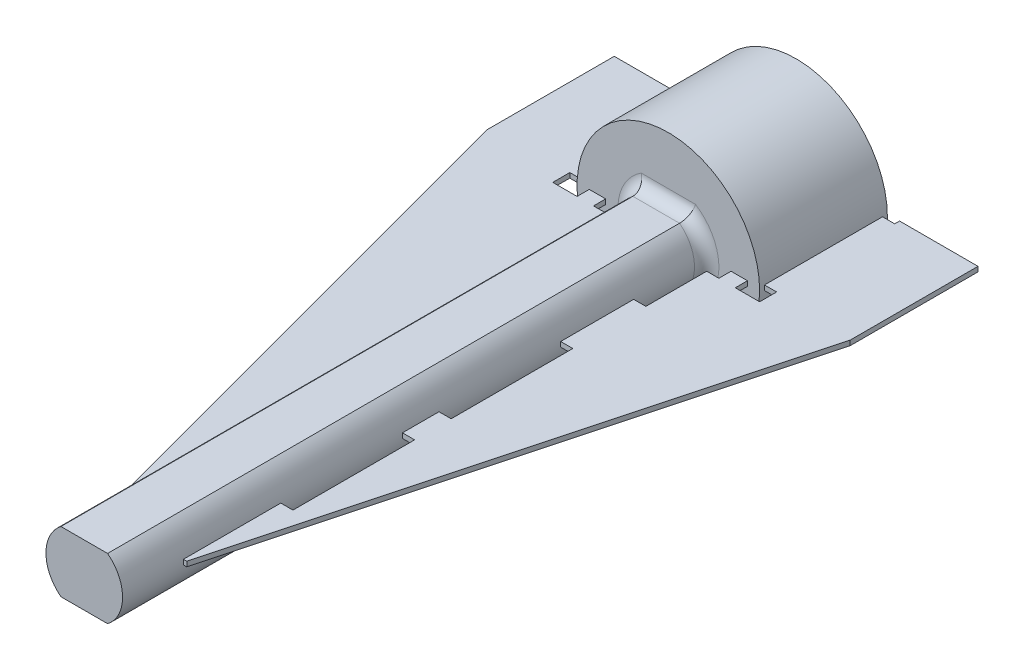
SolidWorks part; units mm, degrees
material "Polylactic Acid (PLA)"
ref_plane "Front Plane" through (0, 0, 0) normal (0, 0, 1) x (1, 0, 0)
ref_plane "Top Plane" through (0, 0, 0) normal (0, 1, 0) x (1, 0, 0)
ref_plane "Right Plane" through (0, 0, 0) normal (1, 0, 0) x (0, 0, -1)
sketch "Sketch2" plane through (0, 0, 0) normal (0, 0, 1) x (1, 0, 0)
  arc A0 (-180.9646, 16.9181) -> (-181.2813, 16.5945) centre (-180.7258, 16.3677) ccw
  arc A1 (-181.2813, 16.5945) -> (-181.4587, 15.6283) centre (-179.0594, 15.6871) ccw
  arc A2 (-181.4587, 15.6283) -> (-180.9368, 15.2683) centre (-178.5779, 19.2465) ccw
  arc A3 (-180.9368, 15.2683) -> (-180.0966, 15.7774) centre (-181.7341, 17.532) ccw
  arc A4 (-180.0966, 15.7774) -> (-179.9066, 16.1884) centre (-180.506, 16.216) ccw
  arc A5 (-179.7695, 16.2766) -> (-179.9066, 16.1884) centre (-179.8067, 16.1838) ccw
  arc A6 (-179.7695, 16.2766) -> (-179.5312, 16.1918) centre (-178.5779, 19.2465) ccw
  arc A7 (-179.4806, 16.0368) -> (-179.5312, 16.1918) centre (-179.561, 16.0963) ccw
  arc A8 (-179.4806, 16.0368) -> (-179.5931, 15.5981) centre (-178.9987, 15.6794) ccw
  arc A9 (-179.5931, 15.5981) -> (-179.2637, 14.6726) centre (-177.2152, 15.9232) ccw
  arc A10 (-179.2637, 14.6726) -> (-178.6317, 14.6218) centre (-178.5779, 19.2465) ccw
  arc A11 (-178.6317, 14.6218) -> (-178.1586, 15.4828) centre (-180.454, 16.1836) ccw
  arc A12 (-178.1586, 15.4828) -> (-178.1996, 15.9338) centre (-178.7324, 15.658) ccw
  arc A13 (-178.1249, 16.0787) -> (-178.1996, 15.9338) centre (-178.1108, 15.9797) ccw
  arc A14 (-178.1249, 16.0787) -> (-177.8761, 16.1244) centre (-178.5779, 19.2465) ccw
  arc A15 (-177.7548, 16.0154) -> (-177.8761, 16.1244) centre (-177.8542, 16.0268) ccw
  arc A16 (-177.7548, 16.0154) -> (-177.6329, 15.5793) centre (-177.1587, 15.9469) ccw
  arc A17 (-177.6329, 15.5793) -> (-176.8848, 14.9425) centre (-175.7362, 17.0498) ccw
  arc A18 (-176.8848, 14.9425) -> (-176.3121, 15.2145) centre (-178.5779, 19.2465) ccw
  arc A19 (-176.3121, 15.2145) -> (-176.3329, 16.1967) centre (-178.6712, 15.6559) ccw
  arc A20 (-176.3329, 16.1967) -> (-176.5939, 16.5668) centre (-176.9175, 16.0615) ccw
  arc A21 (-176.6017, 16.7296) -> (-176.5939, 16.5668) centre (-176.54, 16.651) ccw
  arc A22 (-176.6017, 16.7296) -> (-176.4091, 16.8936) centre (-178.5779, 19.2465) ccw
  arc A23 (-176.2496, 16.8599) -> (-176.4091, 16.8936) centre (-176.3413, 16.8201) ccw
  arc A24 (-176.2496, 16.8599) -> (-175.926, 16.5431) centre (-175.6991, 17.0986) ccw
  arc A25 (-175.926, 16.5431) -> (-174.9597, 16.3657) centre (-175.0185, 18.765) ccw
  arc A26 (-174.9597, 16.3657) -> (-174.5997, 16.8876) centre (-178.5779, 19.2465) ccw
  arc A27 (-174.5997, 16.8876) -> (-175.1088, 17.7278) centre (-176.8634, 16.0903) ccw
  arc A28 (-175.1088, 17.7278) -> (-175.5198, 17.9178) centre (-175.5475, 17.3184) ccw
  arc A29 (-175.608, 18.0549) -> (-175.5198, 17.9178) centre (-175.5152, 18.0177) ccw
  arc A30 (-175.608, 18.0549) -> (-175.5232, 18.2932) centre (-178.5779, 19.2465) ccw
  arc A31 (-175.3682, 18.3438) -> (-175.5232, 18.2932) centre (-175.4277, 18.2635) ccw
  arc A32 (-175.3682, 18.3438) -> (-174.9296, 18.2313) centre (-175.0108, 18.8258) ccw
  arc A33 (-174.9296, 18.2313) -> (-174.004, 18.5608) centre (-175.2546, 20.6092) ccw
  arc A34 (-174.004, 18.5608) -> (-173.9532, 19.1927) centre (-178.5779, 19.2465) ccw
  arc A35 (-173.9532, 19.1927) -> (-174.8142, 19.6658) centre (-175.515, 17.3704) ccw
  arc A36 (-174.8142, 19.6658) -> (-175.2652, 19.6248) centre (-174.9894, 19.092) ccw
  arc A37 (-175.4102, 19.6995) -> (-175.2652, 19.6248) centre (-175.3112, 19.7137) ccw
  arc A38 (-175.4102, 19.6995) -> (-175.4558, 19.9483) centre (-178.5779, 19.2465) ccw
  arc A39 (-175.3469, 20.0696) -> (-175.4558, 19.9483) centre (-175.3583, 19.9702) ccw
  arc A40 (-175.3469, 20.0696) -> (-174.9108, 20.1915) centre (-175.2784, 20.6657) ccw
  arc A41 (-174.9108, 20.1915) -> (-174.274, 20.9396) centre (-176.3812, 22.0882) ccw
  arc A42 (-174.274, 20.9396) -> (-174.5459, 21.5123) centre (-178.5779, 19.2465) ccw
  arc A43 (-174.5459, 21.5123) -> (-175.5282, 21.4915) centre (-174.9873, 19.1532) ccw
  arc A44 (-175.5282, 21.4915) -> (-175.8982, 21.2305) centre (-175.3929, 20.9069) ccw
  arc A45 (-176.0611, 21.2227) -> (-175.8982, 21.2305) centre (-175.9824, 21.2845) ccw
  arc A46 (-176.0611, 21.2227) -> (-176.225, 21.4153) centre (-178.5779, 19.2465) ccw
  arc A47 (-176.1913, 21.5749) -> (-176.225, 21.4153) centre (-176.1515, 21.4831) ccw
  arc A48 (-176.1913, 21.5749) -> (-175.8746, 21.8985) centre (-176.43, 22.1253) ccw
  arc A49 (-175.8746, 21.8985) -> (-175.6971, 22.8647) centre (-178.0964, 22.8059) ccw
  arc A50 (-175.6971, 22.8647) -> (-176.219, 23.2247) centre (-178.5779, 19.2465) ccw
  arc A51 (-176.219, 23.2247) -> (-177.0592, 22.7156) centre (-175.4217, 20.961) ccw
  arc A52 (-177.0592, 22.7156) -> (-177.2492, 22.3046) centre (-176.6499, 22.277) ccw
  arc A53 (-177.3864, 22.2164) -> (-177.2492, 22.3046) centre (-177.3491, 22.3092) ccw
  arc A54 (-177.3864, 22.2164) -> (-177.6247, 22.3012) centre (-178.5779, 19.2465) ccw
  arc A55 (-177.6752, 22.4562) -> (-177.6247, 22.3012) centre (-177.5949, 22.3967) ccw
  arc A56 (-177.6752, 22.4562) -> (-177.5627, 22.8948) centre (-178.1572, 22.8136) ccw
  arc A57 (-177.5627, 22.8948) -> (-177.8922, 23.8204) centre (-179.9406, 22.5698) ccw
  arc A58 (-177.8922, 23.8204) -> (-178.5242, 23.8712) centre (-178.5779, 19.2465) ccw
  arc A59 (-178.5242, 23.8712) -> (-178.9973, 23.0102) centre (-176.7018, 22.3094) ccw
  arc A60 (-178.9973, 23.0102) -> (-178.9563, 22.5592) centre (-178.4234, 22.835) ccw
  arc A61 (-179.0309, 22.4143) -> (-178.9563, 22.5592) centre (-179.0451, 22.5133) ccw
  arc A62 (-179.0309, 22.4143) -> (-179.2797, 22.3686) centre (-178.5779, 19.2465) ccw
  arc A63 (-179.401, 22.4776) -> (-179.2797, 22.3686) centre (-179.3017, 22.4661) ccw
  arc A64 (-179.401, 22.4776) -> (-179.5229, 22.9137) centre (-179.9971, 22.546) ccw
  arc A65 (-179.5229, 22.9137) -> (-180.271, 23.5505) centre (-181.4197, 21.4432) ccw
  arc A66 (-180.271, 23.5505) -> (-180.8437, 23.2785) centre (-178.5779, 19.2465) ccw
  arc A67 (-180.8437, 23.2785) -> (-180.8229, 22.2963) centre (-178.4846, 22.8371) ccw
  arc A68 (-180.8229, 22.2963) -> (-180.562, 21.9262) centre (-180.2383, 22.4315) ccw
  arc A69 (-180.5541, 21.7634) -> (-180.562, 21.9262) centre (-180.6159, 21.842) ccw
  arc A70 (-180.5541, 21.7634) -> (-180.7468, 21.5994) centre (-178.5779, 19.2465) ccw
  arc A71 (-180.9063, 21.6331) -> (-180.7468, 21.5994) centre (-180.8145, 21.6729) ccw
  arc A72 (-180.9063, 21.6331) -> (-181.2299, 21.9499) centre (-181.4567, 21.3944) ccw
  arc A73 (-181.2299, 21.9499) -> (-182.1962, 22.1273) centre (-182.1373, 19.728) ccw
  arc A74 (-182.1962, 22.1273) -> (-182.5561, 21.6054) centre (-178.5779, 19.2465) ccw
  arc A75 (-182.5561, 21.6054) -> (-182.047, 20.7652) centre (-180.2924, 22.4027) ccw
  arc A76 (-182.047, 20.7652) -> (-181.636, 20.5752) centre (-181.6084, 21.1746) ccw
  arc A77 (-181.5478, 20.4381) -> (-181.636, 20.5752) centre (-181.6406, 20.4753) ccw
  arc A78 (-181.5478, 20.4381) -> (-181.6326, 20.1997) centre (-178.5779, 19.2465) ccw
  arc A79 (-181.7877, 20.1492) -> (-181.6326, 20.1997) centre (-181.7281, 20.2295) ccw
  arc A80 (-181.7877, 20.1492) -> (-182.2263, 20.2617) centre (-182.145, 19.6672) ccw
  arc A81 (-182.2263, 20.2617) -> (-183.1518, 19.9322) centre (-181.9012, 17.8838) ccw
  arc A82 (-183.1518, 19.9322) -> (-183.2026, 19.3002) centre (-178.5779, 19.2465) ccw
  arc A83 (-183.2026, 19.3002) -> (-182.3416, 18.8272) centre (-181.6408, 21.1226) ccw
  arc A84 (-182.3416, 18.8272) -> (-181.8906, 18.8681) centre (-182.1664, 19.401) ccw
  arc A85 (-181.7457, 18.7935) -> (-181.8906, 18.8681) centre (-181.8447, 18.7793) ccw
  arc A86 (-181.7457, 18.7935) -> (-181.7, 18.5447) centre (-178.5779, 19.2465) ccw
  arc A87 (-181.809, 18.4234) -> (-181.7, 18.5447) centre (-181.7976, 18.5227) ccw
  arc A88 (-181.809, 18.4234) -> (-182.2451, 18.3015) centre (-181.8775, 17.8273) ccw
  arc A89 (-182.2451, 18.3015) -> (-182.8819, 17.5534) centre (-180.7746, 16.4047) ccw
  arc A90 (-182.8819, 17.5534) -> (-182.6099, 16.9807) centre (-178.5779, 19.2465) ccw
  arc A91 (-182.6099, 16.9807) -> (-181.6277, 17.0015) centre (-182.1685, 19.3398) ccw
  arc A92 (-181.6277, 17.0015) -> (-181.2576, 17.2625) centre (-181.7629, 17.5861) ccw
  arc A93 (-181.0948, 17.2703) -> (-181.2576, 17.2625) centre (-181.1734, 17.2085) ccw
  arc A94 (-181.0948, 17.2703) -> (-180.9308, 17.0777) centre (-178.5779, 19.2465) ccw
  arc A95 (-180.9646, 16.9181) -> (-180.9308, 17.0777) centre (-181.0043, 17.0099) ccw
  arc A96 (-180.9248, 16.8264) -> (-181.1887, 16.5567) centre (-180.7258, 16.3677) ccw
  arc A97 (-181.1887, 16.5567) -> (-181.3594, 15.6773) centre (-179.0594, 15.6871) ccw
  arc A98 (-181.3594, 15.6773) -> (-180.9262, 15.3785) centre (-178.5779, 19.2465) ccw
  arc A99 (-180.9262, 15.3785) -> (-180.1648, 15.8505) centre (-181.7341, 17.532) ccw
  arc A100 (-180.1648, 15.8505) -> (-180.0065, 16.193) centre (-180.506, 16.216) ccw
  arc A101 (-179.7323, 16.3694) -> (-180.0065, 16.193) centre (-179.8067, 16.1838) ccw
  arc A102 (-179.7323, 16.3694) -> (-179.5014, 16.2872) centre (-178.5779, 19.2465) ccw
  arc A103 (-179.4003, 15.9772) -> (-179.5014, 16.2872) centre (-179.561, 16.0963) ccw
  arc A104 (-179.4003, 15.9772) -> (-179.494, 15.6117) centre (-178.9987, 15.6794) ccw
  arc A105 (-179.494, 15.6117) -> (-179.2022, 14.7648) centre (-177.2152, 15.9232) ccw
  arc A106 (-179.2022, 14.7648) -> (-178.6776, 14.7226) centre (-178.5779, 19.2465) ccw
  arc A107 (-178.6776, 14.7226) -> (-178.2542, 15.512) centre (-180.454, 16.1836) ccw
  arc A108 (-178.2542, 15.512) -> (-178.2884, 15.8878) centre (-178.7324, 15.658) ccw
  arc A109 (-178.1391, 16.1777) -> (-178.2884, 15.8878) centre (-178.1108, 15.9797) ccw
  arc A110 (-178.1391, 16.1777) -> (-177.898, 16.222) centre (-178.5779, 19.2465) ccw
  arc A111 (-177.6555, 16.004) -> (-177.898, 16.222) centre (-177.8542, 16.0268) ccw
  arc A112 (-177.6555, 16.004) -> (-177.5539, 15.6406) centre (-177.1587, 15.9469) ccw
  arc A113 (-177.5539, 15.6406) -> (-176.8777, 15.0531) centre (-175.7362, 17.0498) ccw
  arc A114 (-176.8777, 15.0531) -> (-176.4023, 15.2788) centre (-178.5779, 19.2465) ccw
  arc A115 (-176.4023, 15.2788) -> (-176.4304, 16.1742) centre (-178.6712, 15.6559) ccw
  arc A116 (-176.4304, 16.1742) -> (-176.6478, 16.4826) centre (-176.9175, 16.0615) ccw
  arc A117 (-176.6635, 16.8083) -> (-176.6478, 16.4826) centre (-176.54, 16.651) ccw
  arc A118 (-176.6635, 16.8083) -> (-176.4769, 16.9671) centre (-178.5779, 19.2465) ccw
  arc A119 (-176.1578, 16.8996) -> (-176.4769, 16.9671) centre (-176.3413, 16.8201) ccw
  arc A120 (-176.1578, 16.8996) -> (-175.8881, 16.6357) centre (-175.6991, 17.0986) ccw
  arc A121 (-175.8881, 16.6357) -> (-175.0088, 16.465) centre (-175.0185, 18.765) ccw
  arc A122 (-175.0088, 16.465) -> (-174.71, 16.8982) centre (-178.5779, 19.2465) ccw
  arc A123 (-174.71, 16.8982) -> (-175.1819, 17.6596) centre (-176.8634, 16.0903) ccw
  arc A124 (-175.1819, 17.6596) -> (-175.5244, 17.8179) centre (-175.5475, 17.3184) ccw
  arc A125 (-175.7009, 18.0922) -> (-175.5244, 17.8179) centre (-175.5152, 18.0177) ccw
  arc A126 (-175.7009, 18.0922) -> (-175.6187, 18.323) centre (-178.5779, 19.2465) ccw
  arc A127 (-175.3086, 18.4241) -> (-175.6187, 18.323) centre (-175.4277, 18.2635) ccw
  arc A128 (-175.3086, 18.4241) -> (-174.9431, 18.3304) centre (-175.0108, 18.8258) ccw
  arc A129 (-174.9431, 18.3304) -> (-174.0962, 18.6222) centre (-175.2546, 20.6092) ccw
  arc A130 (-174.0962, 18.6222) -> (-174.054, 19.1468) centre (-178.5779, 19.2465) ccw
  arc A131 (-174.054, 19.1468) -> (-174.8434, 19.5702) centre (-175.515, 17.3704) ccw
  arc A132 (-174.8434, 19.5702) -> (-175.2192, 19.536) centre (-174.9894, 19.092) ccw
  arc A133 (-175.5091, 19.6853) -> (-175.2192, 19.536) centre (-175.3112, 19.7137) ccw
  arc A134 (-175.5091, 19.6853) -> (-175.5534, 19.9264) centre (-178.5779, 19.2465) ccw
  arc A135 (-175.3354, 20.1689) -> (-175.5534, 19.9264) centre (-175.3583, 19.9702) ccw
  arc A136 (-175.3354, 20.1689) -> (-174.972, 20.2705) centre (-175.2784, 20.6657) ccw
  arc A137 (-174.972, 20.2705) -> (-174.3845, 20.9467) centre (-176.3812, 22.0882) ccw
  arc A138 (-174.3845, 20.9467) -> (-174.6103, 21.4221) centre (-178.5779, 19.2465) ccw
  arc A139 (-174.6103, 21.4221) -> (-175.5056, 21.3941) centre (-174.9873, 19.1532) ccw
  arc A140 (-175.5056, 21.3941) -> (-175.814, 21.1766) centre (-175.3929, 20.9069) ccw
  arc A141 (-176.1397, 21.1609) -> (-175.814, 21.1766) centre (-175.9824, 21.2845) ccw
  arc A142 (-176.1397, 21.1609) -> (-176.2986, 21.3476) centre (-178.5779, 19.2465) ccw
  arc A143 (-176.2311, 21.6666) -> (-176.2986, 21.3476) centre (-176.1515, 21.4831) ccw
  arc A144 (-176.2311, 21.6666) -> (-175.9671, 21.9363) centre (-176.43, 22.1253) ccw
  arc A145 (-175.9671, 21.9363) -> (-175.7964, 22.8156) centre (-178.0964, 22.8059) ccw
  arc A146 (-175.7964, 22.8156) -> (-176.2296, 23.1145) centre (-178.5779, 19.2465) ccw
  arc A147 (-176.2296, 23.1145) -> (-176.991, 22.6425) centre (-175.4217, 20.961) ccw
  arc A148 (-176.991, 22.6425) -> (-177.1493, 22.3) centre (-176.6499, 22.277) ccw
  arc A149 (-177.4236, 22.1236) -> (-177.1493, 22.3) centre (-177.3491, 22.3092) ccw
  arc A150 (-177.4236, 22.1236) -> (-177.6545, 22.2058) centre (-178.5779, 19.2465) ccw
  arc A151 (-177.7555, 22.5158) -> (-177.6545, 22.2058) centre (-177.5949, 22.3967) ccw
  arc A152 (-177.7555, 22.5158) -> (-177.6618, 22.8813) centre (-178.1572, 22.8136) ccw
  arc A153 (-177.6618, 22.8813) -> (-177.9536, 23.7282) centre (-179.9406, 22.5698) ccw
  arc A154 (-177.9536, 23.7282) -> (-178.4782, 23.7704) centre (-178.5779, 19.2465) ccw
  arc A155 (-178.4782, 23.7704) -> (-178.9016, 22.981) centre (-176.7018, 22.3094) ccw
  arc A156 (-178.9016, 22.981) -> (-178.8675, 22.6052) centre (-178.4234, 22.835) ccw
  arc A157 (-179.0168, 22.3153) -> (-178.8675, 22.6052) centre (-179.0451, 22.5133) ccw
  arc A158 (-179.0168, 22.3153) -> (-179.2578, 22.271) centre (-178.5779, 19.2465) ccw
  arc A159 (-179.5004, 22.489) -> (-179.2578, 22.271) centre (-179.3017, 22.4661) ccw
  arc A160 (-179.5004, 22.489) -> (-179.6019, 22.8524) centre (-179.9971, 22.546) ccw
  arc A161 (-179.6019, 22.8524) -> (-180.2781, 23.4399) centre (-181.4197, 21.4432) ccw
  arc A162 (-180.2781, 23.4399) -> (-180.7535, 23.2142) centre (-178.5779, 19.2465) ccw
  arc A163 (-180.7535, 23.2142) -> (-180.7255, 22.3188) centre (-178.4846, 22.8371) ccw
  arc A164 (-180.7255, 22.3188) -> (-180.508, 22.0104) centre (-180.2383, 22.4315) ccw
  arc A165 (-180.4924, 21.6847) -> (-180.508, 22.0104) centre (-180.6159, 21.842) ccw
  arc A166 (-180.4924, 21.6847) -> (-180.679, 21.5259) centre (-178.5779, 19.2465) ccw
  arc A167 (-180.998, 21.5933) -> (-180.679, 21.5259) centre (-180.8145, 21.6729) ccw
  arc A168 (-180.998, 21.5933) -> (-181.2677, 21.8573) centre (-181.4567, 21.3944) ccw
  arc A169 (-181.2677, 21.8573) -> (-182.1471, 22.028) centre (-182.1373, 19.728) ccw
  arc A170 (-182.1471, 22.028) -> (-182.4459, 21.5948) centre (-178.5779, 19.2465) ccw
  arc A171 (-182.4459, 21.5948) -> (-181.9739, 20.8334) centre (-180.2924, 22.4027) ccw
  arc A172 (-181.9739, 20.8334) -> (-181.6314, 20.6751) centre (-181.6084, 21.1746) ccw
  arc A173 (-181.455, 20.4008) -> (-181.6314, 20.6751) centre (-181.6406, 20.4753) ccw
  arc A174 (-181.455, 20.4008) -> (-181.5372, 20.17) centre (-178.5779, 19.2465) ccw
  arc A175 (-181.8472, 20.0689) -> (-181.5372, 20.17) centre (-181.7281, 20.2295) ccw
  arc A176 (-181.8472, 20.0689) -> (-182.2127, 20.1626) centre (-182.145, 19.6672) ccw
  arc A177 (-182.2127, 20.1626) -> (-183.0597, 19.8708) centre (-181.9012, 17.8838) ccw
  arc A178 (-183.0597, 19.8708) -> (-183.1018, 19.3462) centre (-178.5779, 19.2465) ccw
  arc A179 (-183.1018, 19.3462) -> (-182.3124, 18.9228) centre (-181.6408, 21.1226) ccw
  arc A180 (-182.3124, 18.9228) -> (-181.9366, 18.9569) centre (-182.1664, 19.401) ccw
  arc A181 (-181.6467, 18.8076) -> (-181.9366, 18.9569) centre (-181.8447, 18.7793) ccw
  arc A182 (-181.6467, 18.8076) -> (-181.6024, 18.5666) centre (-178.5779, 19.2465) ccw
  arc A183 (-181.8204, 18.324) -> (-181.6024, 18.5666) centre (-181.7976, 18.5227) ccw
  arc A184 (-181.8204, 18.324) -> (-182.1838, 18.2225) centre (-181.8775, 17.8273) ccw
  arc A185 (-182.1838, 18.2225) -> (-182.7714, 17.5463) centre (-180.7746, 16.4047) ccw
  arc A186 (-182.7714, 17.5463) -> (-182.5456, 17.0709) centre (-178.5779, 19.2465) ccw
  arc A187 (-182.5456, 17.0709) -> (-181.6502, 17.0989) centre (-182.1685, 19.3398) ccw
  arc A188 (-181.6502, 17.0989) -> (-181.3419, 17.3164) centre (-181.7629, 17.5861) ccw
  arc A189 (-181.0161, 17.332) -> (-181.3419, 17.3164) centre (-181.1734, 17.2085) ccw
  arc A190 (-181.0161, 17.332) -> (-180.8573, 17.1454) centre (-178.5779, 19.2465) ccw
  arc A191 (-180.9248, 16.8264) -> (-180.8573, 17.1454) centre (-181.0043, 17.0099) ccw
  arc A192 (-180.9248, 16.8264) -> (-181.1887, 16.5567) centre (-180.7258, 16.3677) ccw construction
  arc A193 (-181.1887, 16.5567) -> (-181.3594, 15.6773) centre (-179.0594, 15.6871) ccw construction
  arc A194 (-181.3594, 15.6773) -> (-180.9262, 15.3785) centre (-178.5779, 19.2465) ccw construction
  arc A195 (-180.9262, 15.3785) -> (-180.1648, 15.8505) centre (-181.7341, 17.532) ccw construction
  arc A196 (-180.1648, 15.8505) -> (-180.0065, 16.193) centre (-180.506, 16.216) ccw construction
  arc A197 (-179.7323, 16.3694) -> (-180.0065, 16.193) centre (-179.8067, 16.1838) ccw construction
  arc A198 (-179.7323, 16.3694) -> (-179.5014, 16.2872) centre (-178.5779, 19.2465) ccw construction
  arc A199 (-179.4003, 15.9772) -> (-179.5014, 16.2872) centre (-179.561, 16.0963) ccw construction
  arc A200 (-179.4003, 15.9772) -> (-179.494, 15.6117) centre (-178.9987, 15.6794) ccw construction
  arc A201 (-179.494, 15.6117) -> (-179.2022, 14.7648) centre (-177.2152, 15.9232) ccw construction
  arc A202 (-179.2022, 14.7648) -> (-178.6776, 14.7226) centre (-178.5779, 19.2465) ccw construction
  arc A203 (-178.6776, 14.7226) -> (-178.2542, 15.512) centre (-180.454, 16.1836) ccw construction
  arc A204 (-178.2542, 15.512) -> (-178.2884, 15.8878) centre (-178.7324, 15.658) ccw construction
  arc A205 (-178.1391, 16.1777) -> (-178.2884, 15.8878) centre (-178.1108, 15.9797) ccw construction
  arc A206 (-178.1391, 16.1777) -> (-177.898, 16.222) centre (-178.5779, 19.2465) ccw construction
  arc A207 (-177.6555, 16.004) -> (-177.898, 16.222) centre (-177.8542, 16.0268) ccw construction
  arc A208 (-177.6555, 16.004) -> (-177.5539, 15.6406) centre (-177.1587, 15.9469) ccw construction
  arc A209 (-177.5539, 15.6406) -> (-176.8777, 15.0531) centre (-175.7362, 17.0498) ccw construction
  arc A210 (-176.8777, 15.0531) -> (-176.4023, 15.2788) centre (-178.5779, 19.2465) ccw construction
  arc A211 (-176.4023, 15.2788) -> (-176.4304, 16.1742) centre (-178.6712, 15.6559) ccw construction
  arc A212 (-176.4304, 16.1742) -> (-176.6478, 16.4826) centre (-176.9175, 16.0615) ccw construction
  arc A213 (-176.6635, 16.8083) -> (-176.6478, 16.4826) centre (-176.54, 16.651) ccw construction
  arc A214 (-176.6635, 16.8083) -> (-176.4769, 16.9671) centre (-178.5779, 19.2465) ccw construction
  arc A215 (-176.1578, 16.8996) -> (-176.4769, 16.9671) centre (-176.3413, 16.8201) ccw construction
  arc A216 (-176.1578, 16.8996) -> (-175.8881, 16.6357) centre (-175.6991, 17.0986) ccw construction
  arc A217 (-175.8881, 16.6357) -> (-175.0088, 16.465) centre (-175.0185, 18.765) ccw construction
  arc A218 (-175.0088, 16.465) -> (-174.71, 16.8982) centre (-178.5779, 19.2465) ccw construction
  arc A219 (-174.71, 16.8982) -> (-175.1819, 17.6596) centre (-176.8634, 16.0903) ccw construction
  arc A220 (-175.1819, 17.6596) -> (-175.5244, 17.8179) centre (-175.5475, 17.3184) ccw construction
  arc A221 (-175.7009, 18.0922) -> (-175.5244, 17.8179) centre (-175.5152, 18.0177) ccw construction
  arc A222 (-175.7009, 18.0922) -> (-175.6187, 18.323) centre (-178.5779, 19.2465) ccw construction
  arc A223 (-175.3086, 18.4241) -> (-175.6187, 18.323) centre (-175.4277, 18.2635) ccw construction
  arc A224 (-175.3086, 18.4241) -> (-174.9431, 18.3304) centre (-175.0108, 18.8258) ccw construction
  arc A225 (-174.9431, 18.3304) -> (-174.0962, 18.6222) centre (-175.2546, 20.6092) ccw construction
  arc A226 (-174.0962, 18.6222) -> (-174.054, 19.1468) centre (-178.5779, 19.2465) ccw construction
  arc A227 (-174.054, 19.1468) -> (-174.8434, 19.5702) centre (-175.515, 17.3704) ccw construction
  arc A228 (-174.8434, 19.5702) -> (-175.2192, 19.536) centre (-174.9894, 19.092) ccw construction
  arc A229 (-175.5091, 19.6853) -> (-175.2192, 19.536) centre (-175.3112, 19.7137) ccw construction
  arc A230 (-175.5091, 19.6853) -> (-175.5534, 19.9264) centre (-178.5779, 19.2465) ccw construction
  arc A231 (-175.3354, 20.1689) -> (-175.5534, 19.9264) centre (-175.3583, 19.9702) ccw construction
  arc A232 (-175.3354, 20.1689) -> (-174.972, 20.2705) centre (-175.2784, 20.6657) ccw construction
  arc A233 (-174.972, 20.2705) -> (-174.3845, 20.9467) centre (-176.3812, 22.0882) ccw construction
  arc A234 (-174.3845, 20.9467) -> (-174.6103, 21.4221) centre (-178.5779, 19.2465) ccw construction
  arc A235 (-174.6103, 21.4221) -> (-175.5056, 21.3941) centre (-174.9873, 19.1532) ccw construction
  arc A236 (-175.5056, 21.3941) -> (-175.814, 21.1766) centre (-175.3929, 20.9069) ccw construction
  arc A237 (-176.1397, 21.1609) -> (-175.814, 21.1766) centre (-175.9824, 21.2845) ccw construction
  arc A238 (-176.1397, 21.1609) -> (-176.2986, 21.3476) centre (-178.5779, 19.2465) ccw construction
  arc A239 (-176.2311, 21.6666) -> (-176.2986, 21.3476) centre (-176.1515, 21.4831) ccw construction
  arc A240 (-176.2311, 21.6666) -> (-175.9671, 21.9363) centre (-176.43, 22.1253) ccw construction
  arc A241 (-175.9671, 21.9363) -> (-175.7964, 22.8156) centre (-178.0964, 22.8059) ccw construction
  arc A242 (-175.7964, 22.8156) -> (-176.2296, 23.1145) centre (-178.5779, 19.2465) ccw construction
  arc A243 (-176.2296, 23.1145) -> (-176.991, 22.6425) centre (-175.4217, 20.961) ccw construction
  arc A244 (-176.991, 22.6425) -> (-177.1493, 22.3) centre (-176.6499, 22.277) ccw construction
  arc A245 (-177.4236, 22.1236) -> (-177.1493, 22.3) centre (-177.3491, 22.3092) ccw construction
  arc A246 (-177.4236, 22.1236) -> (-177.6545, 22.2058) centre (-178.5779, 19.2465) ccw construction
  arc A247 (-177.7555, 22.5158) -> (-177.6545, 22.2058) centre (-177.5949, 22.3967) ccw construction
  arc A248 (-177.7555, 22.5158) -> (-177.6618, 22.8813) centre (-178.1572, 22.8136) ccw construction
  arc A249 (-177.6618, 22.8813) -> (-177.9536, 23.7282) centre (-179.9406, 22.5698) ccw construction
  arc A250 (-177.9536, 23.7282) -> (-178.4782, 23.7704) centre (-178.5779, 19.2465) ccw construction
  arc A251 (-178.4782, 23.7704) -> (-178.9016, 22.981) centre (-176.7018, 22.3094) ccw construction
  arc A252 (-178.9016, 22.981) -> (-178.8675, 22.6052) centre (-178.4234, 22.835) ccw construction
  arc A253 (-179.0168, 22.3153) -> (-178.8675, 22.6052) centre (-179.0451, 22.5133) ccw construction
  arc A254 (-179.0168, 22.3153) -> (-179.2578, 22.271) centre (-178.5779, 19.2465) ccw construction
  arc A255 (-179.5004, 22.489) -> (-179.2578, 22.271) centre (-179.3017, 22.4661) ccw construction
  arc A256 (-179.5004, 22.489) -> (-179.6019, 22.8524) centre (-179.9971, 22.546) ccw construction
  arc A257 (-179.6019, 22.8524) -> (-180.2781, 23.4399) centre (-181.4197, 21.4432) ccw construction
  arc A258 (-180.2781, 23.4399) -> (-180.7535, 23.2142) centre (-178.5779, 19.2465) ccw construction
  arc A259 (-180.7535, 23.2142) -> (-180.7255, 22.3188) centre (-178.4846, 22.8371) ccw construction
  arc A260 (-180.7255, 22.3188) -> (-180.508, 22.0104) centre (-180.2383, 22.4315) ccw construction
  arc A261 (-180.4924, 21.6847) -> (-180.508, 22.0104) centre (-180.6159, 21.842) ccw construction
  arc A262 (-180.4924, 21.6847) -> (-180.679, 21.5259) centre (-178.5779, 19.2465) ccw construction
  arc A263 (-180.998, 21.5933) -> (-180.679, 21.5259) centre (-180.8145, 21.6729) ccw construction
  arc A264 (-180.998, 21.5933) -> (-181.2677, 21.8573) centre (-181.4567, 21.3944) ccw construction
  arc A265 (-181.2677, 21.8573) -> (-182.1471, 22.028) centre (-182.1373, 19.728) ccw construction
  arc A266 (-182.1471, 22.028) -> (-182.4459, 21.5948) centre (-178.5779, 19.2465) ccw construction
  arc A267 (-182.4459, 21.5948) -> (-181.9739, 20.8334) centre (-180.2924, 22.4027) ccw construction
  arc A268 (-181.9739, 20.8334) -> (-181.6314, 20.6751) centre (-181.6084, 21.1746) ccw construction
  arc A269 (-181.455, 20.4008) -> (-181.6314, 20.6751) centre (-181.6406, 20.4753) ccw construction
  arc A270 (-181.455, 20.4008) -> (-181.5372, 20.17) centre (-178.5779, 19.2465) ccw construction
  arc A271 (-181.8472, 20.0689) -> (-181.5372, 20.17) centre (-181.7281, 20.2295) ccw construction
  arc A272 (-181.8472, 20.0689) -> (-182.2127, 20.1626) centre (-182.145, 19.6672) ccw construction
  arc A273 (-182.2127, 20.1626) -> (-183.0597, 19.8708) centre (-181.9012, 17.8838) ccw construction
  arc A274 (-183.0597, 19.8708) -> (-183.1018, 19.3462) centre (-178.5779, 19.2465) ccw construction
  arc A275 (-183.1018, 19.3462) -> (-182.3124, 18.9228) centre (-181.6408, 21.1226) ccw construction
  arc A276 (-182.3124, 18.9228) -> (-181.9366, 18.9569) centre (-182.1664, 19.401) ccw construction
  arc A277 (-181.6467, 18.8076) -> (-181.9366, 18.9569) centre (-181.8447, 18.7793) ccw construction
  arc A278 (-181.6467, 18.8076) -> (-181.6024, 18.5666) centre (-178.5779, 19.2465) ccw construction
  arc A279 (-181.8204, 18.324) -> (-181.6024, 18.5666) centre (-181.7976, 18.5227) ccw construction
  arc A280 (-181.8204, 18.324) -> (-182.1838, 18.2225) centre (-181.8775, 17.8273) ccw construction
  arc A281 (-182.1838, 18.2225) -> (-182.7714, 17.5463) centre (-180.7746, 16.4047) ccw construction
  arc A282 (-182.7714, 17.5463) -> (-182.5456, 17.0709) centre (-178.5779, 19.2465) ccw construction
  arc A283 (-182.5456, 17.0709) -> (-181.6502, 17.0989) centre (-182.1685, 19.3398) ccw construction
  arc A284 (-181.6502, 17.0989) -> (-181.3419, 17.3164) centre (-181.7629, 17.5861) ccw construction
  arc A285 (-181.0161, 17.332) -> (-181.3419, 17.3164) centre (-181.1734, 17.2085) ccw construction
  arc A286 (-181.0161, 17.332) -> (-180.8573, 17.1454) centre (-178.5779, 19.2465) ccw construction
  arc A287 (-180.9248, 16.8264) -> (-180.8573, 17.1454) centre (-181.0043, 17.0099) ccw construction
  circle A288 centre (-178.5779, 19.2465) radius 7.5
  dimension "D3" = 15
  dimension "D1" = 0
  dimension "D2" = 0.1
extrude "Boss-Extrude1" add sketch "Sketch2" against normal offset from surface 0.5 and the other way offset from surface (4 mm away) 1
sketch "Sketch4" plane through (0, 0, 4) normal (0, 0, 1) x (1, 0, 0)
  circle A1 centre (-178.5779, 19.2465) radius 7.5
  circle A2 centre (-178.5779, 19.2465) radius 7.5
  dimension "D1" = 0
extrude "Boss-Extrude2" add sketch "Sketch4" along normal blind 1
sketch "Sketch6" plane through (0, 0, 5) normal (0, 0, 1) x (1, 0, 0)
  line L1 (-180.4943, 21.7465) -> (-176.6615, 21.7465)
  line L2 (-180.4943, 21.7465) -> (-180.4943, 16.7465) construction
  line L3 (-180.4943, 16.7465) -> (-176.6615, 16.7465)
  line L4 (-176.6615, 21.7465) -> (-176.6615, 16.7465) construction
  line L5 (-180.4943, 21.7465) -> (-176.6615, 16.7465) construction
  line L6 (-180.4943, 16.7465) -> (-176.6615, 21.7465) construction
  arc A0 (-180.4943, 21.7465) -> (-180.4943, 16.7465) centre (-178.5779, 19.2465) ccw
  arc A1 (-176.6615, 16.7465) -> (-176.6615, 21.7465) centre (-178.5779, 19.2465) ccw
  dimension "D1" = 6.3
  dimension "D2" = 2.5
extrude "Boss-Extrude3" add sketch "Sketch6" along normal blind 48
fillet "Fillet1" radius 1 4 edges at (-181.7279, 19.2465, 5) (-178.5779, 16.7465, 5) (-175.4279, 19.2465, 5) (-178.5779, 21.7465, 5)
ref_plane "Plane1" through (0, 19.2465, 0) normal (0, 1, 0) x (1, 0, 0)
sketch "Sketch7" plane through (0, 19.2465, 0) normal (0, 1, 0) x (1, 0, 0)
  line L1 (-182.7279, -6) -> (-182.7279, -11)
  line L2 (-182.0023, -48) -> (-193.5242, -5)
  line L3 (-187.0779, -6) -> (-185.0779, -6)
  line L5 (-171.0779, 5.5) -> (-186.0779, 5.5) construction
  line L6 (-187.0779, 5.5) -> (-193.5242, 5.5)
  line L7 (-187.0779, 5.5) -> (-187.0779, 5.1)
  line L9 (-193.5242, 5.5) -> (-193.5242, -5)
  line L10 (-186.0779, 5.5) -> (-186.0779, -5) construction
  line L11 (-186.0779, -5) -> (-171.0779, -5) construction
  line L12 (-181.7279, -6) -> (-181.7279, -53) construction
  line L13 (-187.0779, -4.6) -> (-187.0779, -6)
  line L14 (-187.0779, 5.1) -> (-186.0779, 5.1)
  line L16 (-187.0779, -4.6) -> (-186.0779, -4.6)
  line L17 (-186.0779, 5.1) -> (-186.0779, -4.6)
  line L19 (-185.0779, -5) -> (-183.7279, -5)
  line L20 (-185.0779, -5) -> (-185.0779, -6)
  line L22 (-183.7279, -5) -> (-183.7279, -6)
  line L23 (-182.7279, -11) -> (-181.7279, -11)
  line L25 (-182.7279, -17) -> (-181.7279, -17)
  line L26 (-181.7279, -11) -> (-181.7279, -17)
  line L27 (-182.7279, -27) -> (-181.7279, -27)
  line L29 (-182.7279, -30) -> (-181.7279, -30)
  line L30 (-181.7279, -27) -> (-181.7279, -30)
  line L31 (-182.7279, -40) -> (-181.7279, -40)
  line L33 (-182.0023, -48) -> (-181.7279, -48)
  line L34 (-181.7279, -40) -> (-181.7279, -48)
  line L39 (-183.7279, -6) -> (-182.7279, -6)
  line L40 (-182.7279, -17) -> (-182.7279, -27)
  line L41 (-182.7279, -30) -> (-182.7279, -40)
  line L43 (-180.4943, -6) -> (-181.7279, -6) construction
  line L44 (-182.7279, -5) -> (-180.8078, -5) construction
  line L45 (-176.6615, -53) -> (-180.4943, -53) construction
  line L46 (-178.5779, 5.5) -> (-178.5779, -53) construction
  line L47 (-175.1535, -48) -> (-175.4279, -48)
  line L48 (-175.4279, -40) -> (-175.4279, -48)
  line L49 (-174.4279, -40) -> (-175.4279, -40)
  line L50 (-174.4279, -30) -> (-174.4279, -40)
  line L51 (-174.4279, -30) -> (-175.4279, -30)
  line L52 (-175.4279, -27) -> (-175.4279, -30)
  line L53 (-174.4279, -27) -> (-175.4279, -27)
  line L54 (-174.4279, -17) -> (-174.4279, -27)
  line L55 (-174.4279, -17) -> (-175.4279, -17)
  line L56 (-175.4279, -11) -> (-175.4279, -17)
  line L57 (-174.4279, -11) -> (-175.4279, -11)
  line L58 (-174.4279, -6) -> (-174.4279, -11)
  line L59 (-173.4279, -6) -> (-174.4279, -6)
  line L60 (-173.4279, -5) -> (-173.4279, -6)
  line L61 (-172.0779, -5) -> (-173.4279, -5)
  line L62 (-172.0779, -5) -> (-172.0779, -6)
  line L63 (-170.0779, -6) -> (-172.0779, -6)
  line L64 (-170.0779, -4.6) -> (-170.0779, -6)
  line L65 (-170.0779, -4.6) -> (-171.0779, -4.6)
  line L66 (-171.0779, 5.1) -> (-171.0779, -4.6)
  line L67 (-170.0779, 5.1) -> (-171.0779, 5.1)
  line L68 (-170.0779, 5.5) -> (-170.0779, 5.1)
  line L69 (-170.0779, 5.5) -> (-163.6317, 5.5)
  line L70 (-163.6317, 5.5) -> (-163.6317, -5)
  line L71 (-175.1535, -48) -> (-163.6317, -5)
  dimension "D1" = 1
  dimension "D2" = 1
  dimension "D3" = 1
  dimension "D4" = 0.4
  dimension "D5" = 0.4
  dimension "D6" = 1
  dimension "D7" = 1
  dimension "D8" = 5
  dimension "D9" = 10
  dimension "D10" = 10
  dimension "D11" = 5
  dimension "D12" = 12
  dimension "D13" = 25
  dimension "D14" = 15
  dimension "D15" = 15
extrude "Boss-Extrude6" add sketch "Sketch7" along normal mid plane 0.4 separate body
